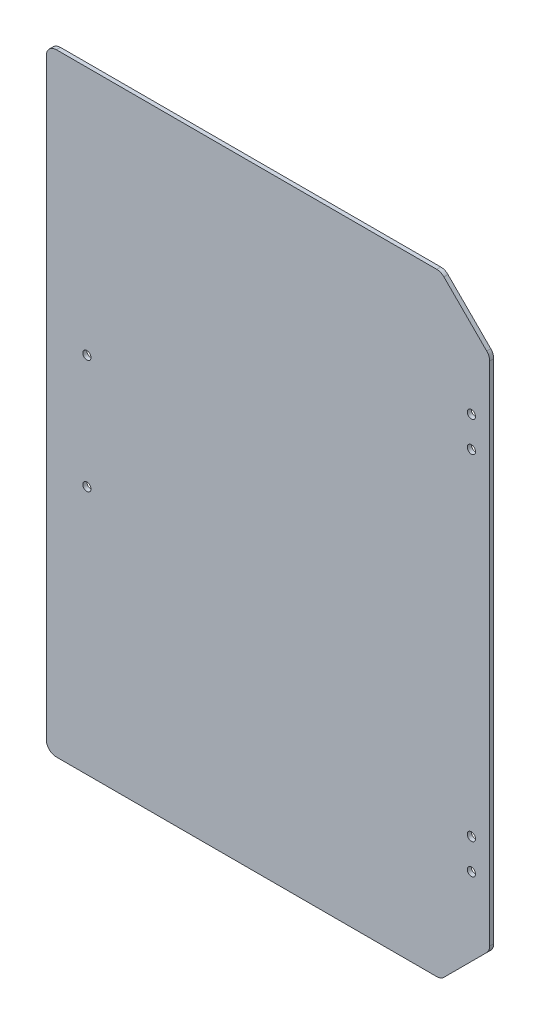
SolidWorks part; units mm, degrees
material "Glass"
ref_plane "Plan de face" through (0, 0, 0) normal (0, 0, 1) x (1, 0, 0)
ref_plane "Plan de dessus" through (0, 0, 0) normal (0, 1, 0) x (1, 0, 0)
ref_plane "Plan de droite" through (0, 0, 0) normal (1, 0, 0) x (0, 0, -1)
sketch "Sketch1" plane through (0, 0, 0) normal (0, 0, 1) x (1, 0, 0)
  line L0 (198.3556, 254.4354) -> (198.3556, -252.5646)
  line L1 (-238.1444, -300.5646) -> (150.3556, -300.5646)
  line L2 (-238.1444, -300.5646) -> (-238.1444, 302.4354)
  line L3 (-238.1444, 302.4354) -> (150.3556, 302.4354)
  line L4 (150.3556, -300.5646) -> (198.3556, -252.5646)
  line L5 (150.3556, 302.4354) -> (198.3556, 254.4354)
  line L6 (-243.1444, 302.4354) -> (-238.1444, 302.4354) construction
  line L7 (-240.6444, 302.4354) -> (-240.6444, -300.5646) construction
  line L8 (180.3556, 195.9354) -> (180.3556, 165.9354) construction
  line L9 (180.3556, -164.0646) -> (180.3556, -194.0646) construction
  circle A0 centre (180.3556, 195.9354) radius 4.05
  circle A1 centre (180.3556, 165.9354) radius 4.05
  circle A2 centre (180.3556, -164.0646) radius 4.05
  circle A3 centre (180.3556, -194.0646) radius 4.05
  point P4 (198.3556, -300.5646)
  point P5 (198.3556, 302.4354)
  point P11 (-240.6444, 180.9354)
  point P14 (-240.6444, -179.0646)
  dimension "D1" = 48
  dimension "D2" = 48
  dimension "D3" = 48
  dimension "D4" = 48
  dimension "D5" = 439
extrude "Boss-Extrude1" add sketch "Sketch1" along normal blind 4
fillet "Fillet1" radius 10 6 edges at (-238.1444, 302.4354, 2) (-238.1444, -300.5646, 2) (150.3556, -300.5646, 2) (198.3556, -252.5646, 2) (198.3556, 254.4354, 2) (150.3556, 302.4354, 2)
sketch "Sketch2" plane through (0, 0, 4) normal (0, 0, 1) x (1, 0, 0)
  line L0 (-238.1444, 0.9354) -> (-123.6999, 0.9354) construction
  line L1 (-238.1444, 292.4354) -> (-238.1444, -290.5646) construction
  circle A0 centre (-198.1444, 56.9354) radius 4.05
  circle A1 centre (-198.1444, -55.0646) radius 4.05
  dimension "D1" = 8.1
  dimension "D2" = 8.1
  dimension "D3" = 112
  dimension "D4" = 112
  dimension "D5" = 40
extrude "Cut-Extrude1" cut sketch "Sketch2" against normal blind 4
